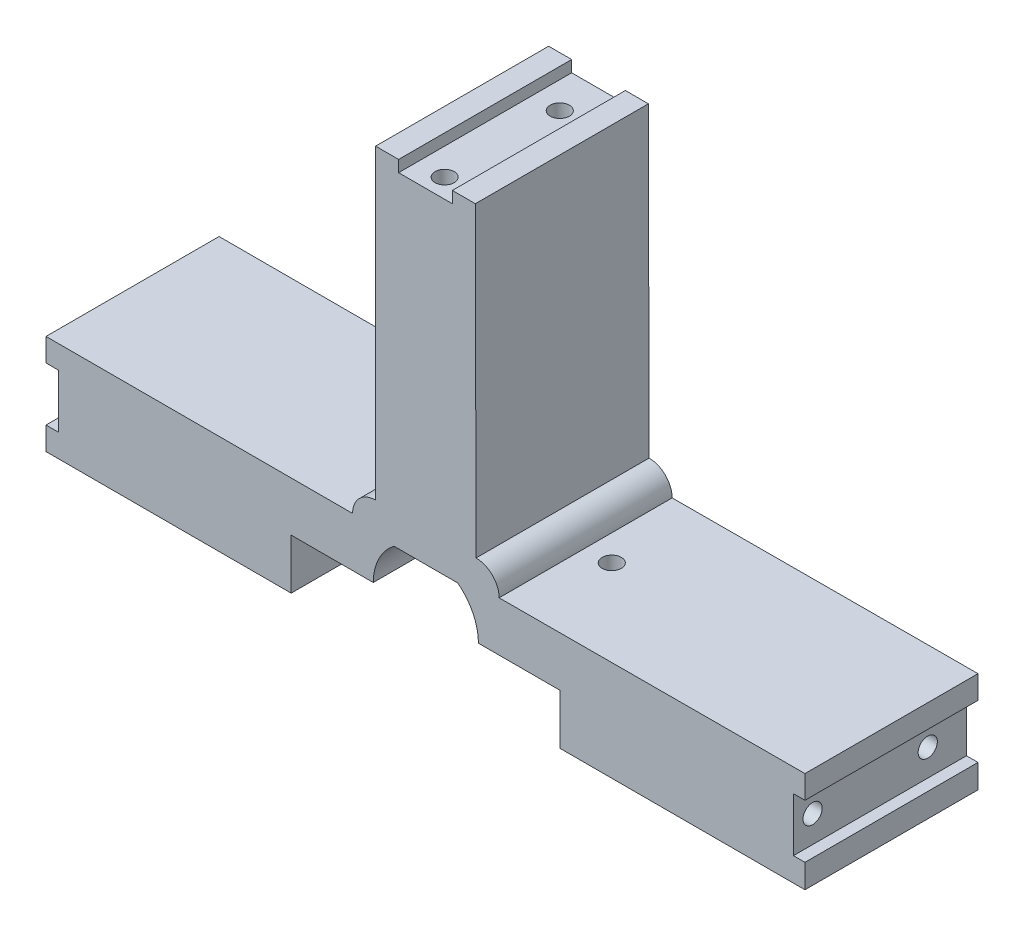
SolidWorks part; units mm, degrees
ref_plane "Front" through (0, 0, 0) normal (0, 0, 1) x (1, 0, 0)
ref_plane "Top" through (0, 0, 0) normal (0, 1, 0) x (1, 0, 0)
ref_plane "Right" through (0, 0, 0) normal (1, 0, 0) x (0, 0, -1)
sketch "Sketch1" plane through (0, 0, 0) normal (0, 0, 1) x (1, 0, 0)
  line L1 (-49.45, 62.225) -> (49.45, 62.225)
  line L2 (-49.45, 62.225) -> (-49.45, -62.225)
  line L3 (-49.45, -62.225) -> (49.45, -62.225)
  line L4 (49.45, 62.225) -> (49.45, -62.225)
  line L5 (-49.45, 62.225) -> (49.45, -62.225) construction
  line L6 (-49.45, -62.225) -> (49.45, 62.225) construction
  point P0 (0, 0)
  dimension "D1" = 124.45
  dimension "D2" = 98.9
extrude "body" add sketch "Sketch1" along normal blind 22.55
sketch "Sketch4" plane through (0, 0, 0) normal (0, 0, -1) x (-1, 0, 0)
  line L0 (-49.45, 62.225) -> (49.45, 62.225) construction
  line L1 (3.5, 60.725) -> (-3.5, 60.725)
  line L2 (3.5, 60.725) -> (3.5, 63.725)
  line L3 (3.5, 63.725) -> (-3.5, 63.725)
  line L4 (-3.5, 60.725) -> (-3.5, 63.725)
  line L5 (3.5, 60.725) -> (-3.5, 63.725) construction
  line L6 (3.5, 63.725) -> (-3.5, 60.725) construction
  line L19 (47.85, 9.275) -> (50.85, 9.275)
  line L20 (47.85, 9.275) -> (47.85, 16.275)
  line L21 (47.85, 16.275) -> (50.85, 16.275)
  line L22 (50.85, 9.275) -> (50.85, 16.275)
  line L23 (-3.6, -35.075) -> (-3.6, -38.075)
  line L24 (-3.6, -35.075) -> (3.4, -35.075)
  line L25 (3.4, -35.075) -> (3.4, -38.075)
  line L26 (-3.6, -38.075) -> (3.4, -38.075)
  line L27 (-47.95, 16.375) -> (-50.95, 16.375)
  line L28 (49.45, 62.225) -> (49.45, -62.225) construction
  line L29 (-47.95, 16.375) -> (-47.95, 9.375)
  line L30 (-47.95, 9.375) -> (-50.95, 9.375)
  line L31 (-50.95, 16.375) -> (-50.95, 9.375)
  circle A0 centre (0, 12.875) radius 27.5
  point P0 (0, 62.225)
  point P9 (49.35, 16.275)
  dimension "D5" = 55
  dimension "D6" = 49.45
  dimension "D1" = 7
  dimension "D2" = 3
  dimension "D4" = 47.85
  dimension "D7" = 47.85
  dimension "D8" = 45.95
  dimension "D3" = 4
extrude "Cut-Extrude1" cut sketch "Sketch4" against normal blind 63 contours L1 L4 L3 L2 | L22 L21 L20 L19 | L29 L30 L31 L27
sketch "Sketch5" plane through (0, 0, 0) normal (0, 0, -1) x (-1, 0, 0)
  line L0 (-47.95, 12.875) -> (47.85, 12.775) construction
  line L1 (-47.95, 16.375) -> (-47.95, 9.375) construction
  line L2 (47.85, 9.275) -> (47.85, 16.275) construction
  line L3 (47.85, 12.775) -> (0, 60.725) construction
  line L4 (3.5, 60.725) -> (-3.5, 60.725) construction
  line L6 (-0.05, 12.825) -> (0, 60.725) construction
  line L8 (-4.1997, 7.375) -> (4.0997, 7.375)
  line L9 (-4.1997, 7.375) -> (-4.1997, 18.275)
  line L10 (-4.1997, 18.275) -> (4.0997, 18.275)
  line L11 (4.0997, 7.375) -> (4.0997, 18.275)
  line L12 (-4.1997, 7.375) -> (4.0997, 18.275) construction
  line L13 (-4.1997, 18.275) -> (4.0997, 7.375) construction
  circle A0 centre (-0.05, 12.825) radius 6.85
  dimension "D1" = 13.7
  dimension "D2" = 5.45
extrude "Cut-Extrude2" cut sketch "Sketch5" against normal blind 63 contours L8 L11 L10 L9 | L11 A0 | L9 A0
sketch "Sketch6" plane through (0, 0, 0) normal (0, 0, -1) x (-1, 0, 0)
  line L0 (47.85, 16.275) -> (49.45, 16.275) construction
  line L1 (49.45, 62.225) -> (6.5, 62.225)
  line L2 (49.45, 62.225) -> (49.45, 19.275)
  line L3 (49.45, 19.275) -> (6.5, 19.275)
  line L4 (6.5, 62.225) -> (6.5, 19.275)
  line L5 (3.5, 60.725) -> (3.5, 62.225) construction
  line L6 (3.5, 60.725) -> (-3.5, 60.725) construction
  line L8 (0, 60.725) -> (-0.05, 18.275) construction
  line L9 (-4.1997, 18.275) -> (4.0997, 18.275) construction
  line L10 (-49.5475, 19.3916) -> (-6.5976, 19.2904)
  line L11 (-6.4964, 62.2403) -> (-6.5976, 19.2904)
  line L12 (-49.4463, 62.3415) -> (-6.4964, 62.2403)
  line L13 (-49.4463, 62.3415) -> (-49.5475, 19.3916)
  line L14 (49.45, 9.275) -> (49.45, -62.225) construction
  line L15 (-49.45, -62.225) -> (49.45, -62.225)
  line L16 (-49.45, -62.225) -> (-49.45, 6.275)
  line L17 (-49.45, 6.275) -> (49.45, 6.275)
  line L18 (49.45, -62.225) -> (49.45, 6.275)
  line L19 (47.85, 9.275) -> (49.45, 9.275) construction
  circle A0 centre (6.5, 19.275) radius 3
  circle A1 centre (-6.5976, 19.2904) radius 3
  point P7 (48.65, 16.275)
  line M15 (49.45, 62.225) -> (3.5, 62.225)
  line M19 (-3.5, 62.225) -> (-49.45, 62.225)
  line M20 (-49.45, 62.225) -> (-49.45, 16.375)
  line M24 (-49.45, 9.375) -> (-49.45, -62.225)
  line M25 (-49.45, -62.225) -> (49.45, -62.225)
  line M26 (49.45, -62.225) -> (49.45, 9.275)
  line M30 (49.45, 16.275) -> (49.45, 62.225)
  dimension "D3" = 6
  dimension "D1" = 3
  dimension "D2" = 3
  dimension "D4" = 3
extrude "Cut-Extrude3" cut sketch "Sketch6" against normal blind 63 contours A0 L3 L4 M30 M15 | L10 A1 L11 L13 M19 M20 | L17 M24 M25 M26
sketch "Sketch7" plane through (49.5929, 0.1168, 0) normal (-1, -0.0024, 0) x (0, 0, 1)
  line L1 (0, 62.1083) -> (22.55, 62.1083)
  line L2 (0, 62.1083) -> (0, 60.6666)
  line L3 (0, 60.6666) -> (22.55, 60.6666)
  line L4 (22.55, 62.1083) -> (22.55, 60.6666)
extrude "Cut-Extrude4" cut sketch "Sketch7" against normal blind 63
sketch "Sketch8" plane through (0, 0, 22.55) normal (0, 0, 1) x (1, 0, 0)
  line L0 (-49.45, 6.275) -> (49.45, 6.275) construction
  line L1 (-17.5, -0.275) -> (17.5, -0.275)
  line L2 (-17.5, -0.275) -> (-17.5, 12.825)
  line L3 (-17.5, 12.825) -> (17.5, 12.825)
  line L4 (17.5, -0.275) -> (17.5, 12.825)
  line L5 (-17.5, -0.275) -> (17.5, 12.825) construction
  line L6 (-17.5, 12.825) -> (17.5, -0.275) construction
  line L7 (6.9, 12.825) -> (-6.8, 12.825) construction
  arc A0 (4.1997, 7.375) -> (4.1997, 18.275) centre (0.05, 12.825) ccw construction
  arc A1 (-4.0997, 18.275) -> (-4.0997, 7.375) centre (0.05, 12.825) ccw construction
  point P0 (0, 6.275)
  dimension "D1" = 0
  dimension "D2" = 35
extrude "Cut-Extrude5" cut sketch "Sketch8" against normal through all
sketch "Sketch9" plane through (0, 12.825, 0) normal (0, -1, 0) x (1, 0, 0)
  line L0 (17.5, 11.275) -> (-17.5, 11.275) construction
  line L1 (17.5, 0) -> (17.5, 22.55) construction
  line L2 (-17.5, 0) -> (-17.5, 22.55) construction
  line L3 (0, 11.275) -> (0, 21.275)
  circle A0 centre (13, 11.275) radius 1.25
  circle A1 centre (-13, 11.275) radius 1.25
  dimension "D2" = 2.5
  dimension "D1" = 10
  dimension "D3" = 4.5
extrude "Cut-Extrude6" cut sketch "Sketch9" against normal blind 10 contours A0 | A1
sketch "Sketch10" plane through (47.95, 0, 0) normal (1, 0, 0) x (0, 0, -1)
  line L0 (0, 12.875) -> (-22.55, 12.875) construction
  line L1 (0, 16.375) -> (0, 9.375) construction
  line L2 (-22.55, 9.375) -> (-22.55, 16.375) construction
  line L3 (-11.275, 12.875) -> (-11.275, 16.375) construction
  line L5 (-22.55, 16.375) -> (0, 16.375) construction
  line L6 (-12.55, 12.875) -> (-12.55, 16.375)
  circle A0 centre (-20.05, 12.875) radius 1.25
  circle A2 centre (-5.05, 12.875) radius 1.25
  dimension "D1" = 2.5
  dimension "D2" = 1.275
  dimension "D3" = 7.5
extrude "Cut-Extrude7" cut sketch "Sketch10" against normal blind 5 contours A0 | A2
pattern_circular "CirPattern1" count 4 every 90 about axis through (0.05, 12.825, 0) along (0, 0, 1) of "Cut-Extrude7"
